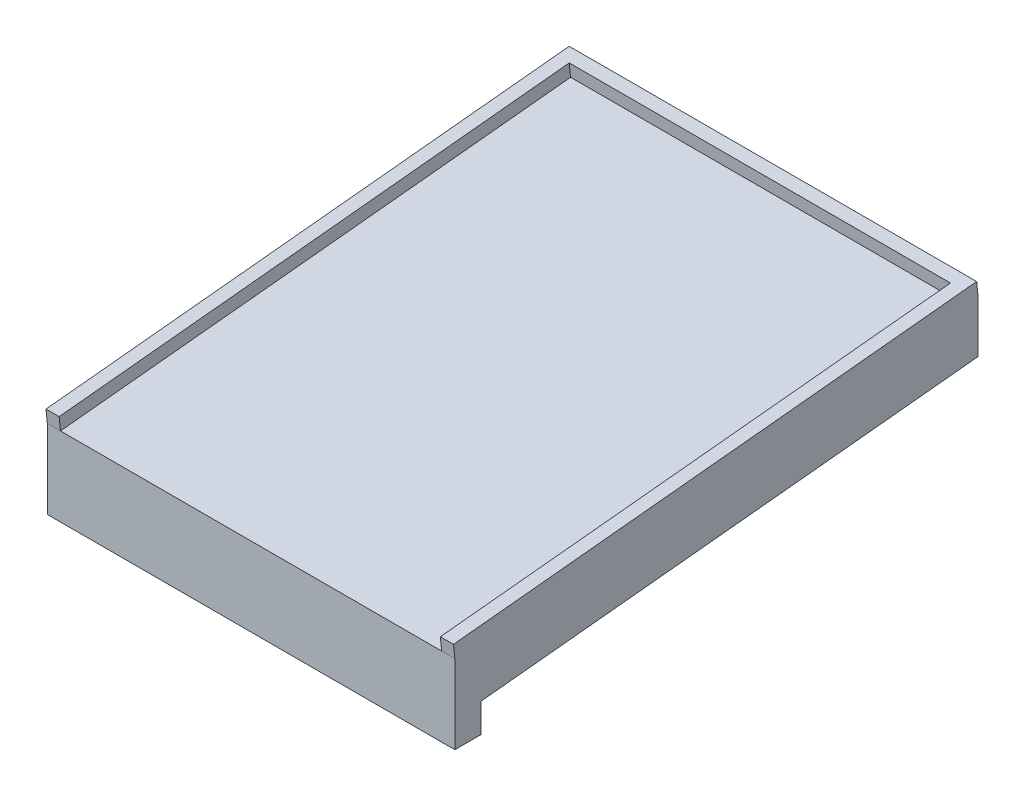
SolidWorks part; units mm, degrees
ref_plane "Front Plane" through (0, 0, 0) normal (0, 0, 1) x (1, 0, 0)
ref_plane "Top Plane" through (0, 0, 0) normal (0, 1, 0) x (1, 0, 0)
ref_plane "Right Plane" through (0, 0, 0) normal (1, 0, 0) x (0, 0, -1)
sketch "Sketch4" plane through (0, 0, 0) normal (1, 0, 0) x (0, 0, -1)
  line L0 (0, 0) -> (0, 20)
  line L1 (0, 0) -> (198.9975, 20)
  line L2 (0, 20) -> (198.9975, 40)
  line L3 (198.9975, 20) -> (198.9975, 40)
  line L4 (0, 27.5) -> (0, -27.5) construction
  dimension "D1" = 20
  dimension "D2" = 200
  dimension "D3" = 20
extrude "Boss-Extrude1" add sketch "Sketch4" along normal blind 155
sketch "Sketch7" plane through (0, 0, 0) normal (0, 0, 1) x (1, 0, 0)
  line L1 (0, 10) -> (155, 10)
  line L2 (0, 10) -> (0, -10)
  line L3 (0, -10) -> (155, -10)
  line L4 (155, 10) -> (155, -10)
  line L5 (0, 20) -> (0, 10) construction
  line L8 (155, 0) -> (155, 20) construction
  dimension "D1" = 20
  dimension "D2" = 10
  dimension "D3" = 155
extrude "Boss-Extrude4" add sketch "Sketch7" against normal blind 10
sketch "Sketch8" plane through (0, 19.8, 1.99) normal (0, 0.995, 0.1) x (1, 0, 0)
  line L0 (155, 2) -> (0, 2) construction
  line L1 (0, 202) -> (5, 202)
  line L2 (0, 202) -> (0, 2)
  line L3 (0, 2) -> (5, 2)
  line L4 (5, 202) -> (5, 2)
  line L6 (150, 2) -> (155, 2)
  line L7 (150, 2) -> (150, 202)
  line L8 (150, 202) -> (155, 202)
  line L9 (155, 2) -> (155, 202)
  line L10 (5, 202) -> (150, 202)
  line L11 (5, 202) -> (5, 197)
  line L12 (5, 197) -> (150, 197)
  line L13 (150, 202) -> (150, 197)
  line M6 (0, 202) -> (0, 2)
  line M7 (0, 2) -> (155, 2)
  line M8 (155, 2) -> (155, 202)
  line M9 (155, 202) -> (0, 202)
  dimension "D1" = 5
  dimension "D2" = 5
extrude "Boss-Extrude5" add sketch "Sketch8" along normal blind 5 contours L4 M9 M6 M7 | L4 L12 L7 M9 | L7 M7 M8 M9
